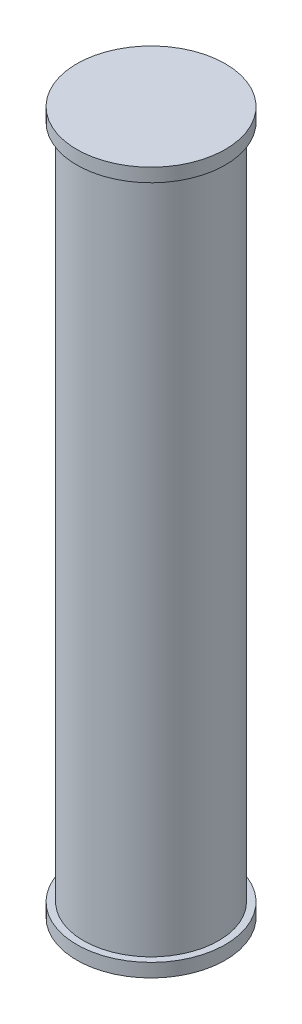
SolidWorks part; units mm, degrees
ref_plane "Front Plane" through (0, 0, 0) normal (0, 0, 1) x (1, 0, 0)
ref_plane "Top Plane" through (0, 0, 0) normal (0, 1, 0) x (1, 0, 0)
ref_plane "Right Plane" through (0, 0, 0) normal (1, 0, 0) x (0, 0, -1)
sketch "Sketch1" plane through (0, 0, 0) normal (0, 1, 0) x (1, 0, 0)
  circle A0 centre (0, 0) radius 1.27
  dimension "D1" = 2.54
extrude "Boss-Extrude1" add sketch "Sketch1" along normal mid plane 12.7
sketch "Sketch2" plane through (0, -6.35, 0) normal (0, -1, 0) x (1, 0, 0)
  circle A0 centre (0, 0) radius 1.397
  dimension "D1" = 2.794
extrude "Boss-Extrude2" add sketch "Sketch2" along normal blind 0.254
mirror "Mirror1" about plane through (0, 0, 0) normal (0, 1, 0) of "Boss-Extrude2"
